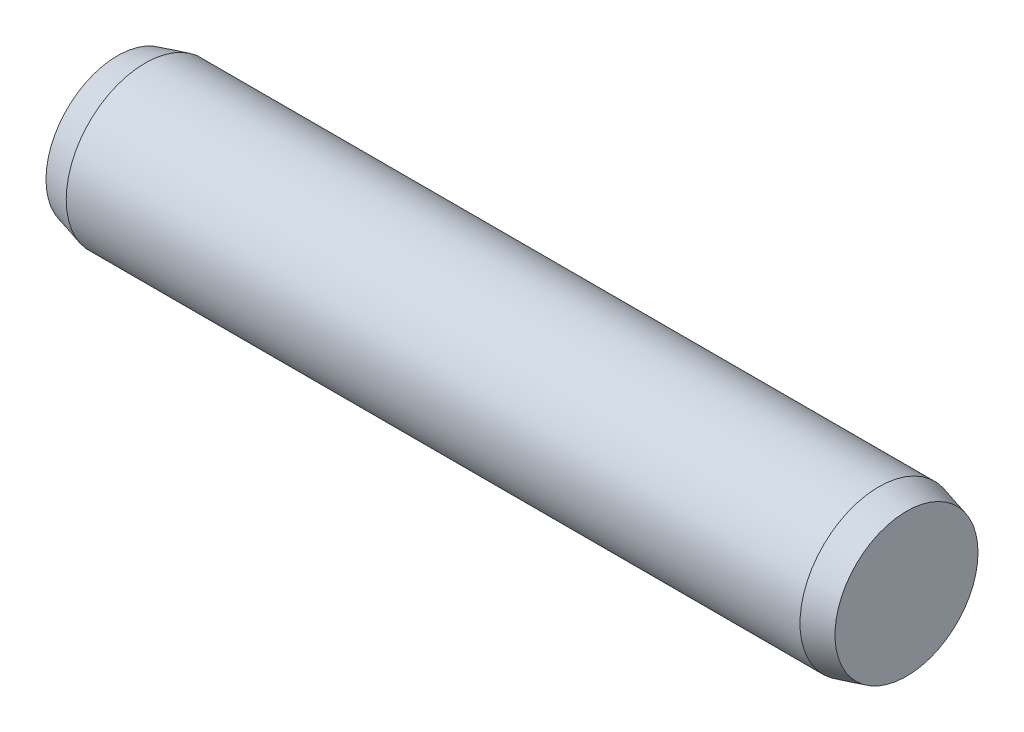
SolidWorks part; units mm, degrees
ref_plane "Front Plane" through (0, 0, 0) normal (0, 0, 1) x (1, 0, 0)
ref_plane "Top Plane" through (0, 0, 0) normal (0, 1, 0) x (1, 0, 0)
ref_plane "Right Plane" through (0, 0, 0) normal (1, 0, 0) x (0, 0, -1)
sketch "Sketch1" plane through (0, 0, 0) normal (0, 0, 1) x (1, 0, 0)
  line L0 (-4.65, 0) -> (4.65, 0) construction
  line L1 (4.65, 1) -> (4.65, -1) construction
  line L2 (-4.65, 1) -> (-4.65, -1) construction
  line L3 (5, 1) -> (5, -1) construction
  line L4 (-5, 1) -> (-5, -1) construction
  line L5 (-4.65, 0) -> (-5, 0) construction
  line L6 (4.65, 0) -> (5, 0) construction
  dimension "Dia" = 2
  dimension "C" = 0.35
  dimension "D1" = 0.35
  dimension "Length" = 10
sketch "Sketch2" plane through (0, 0, 0) normal (1, 0, 0) x (0, 0, -1)
  circle A0 centre (0, 0) radius 1
extrude "Extrude1" add sketch "Sketch2" against normal up to vertex (4.65 mm away) and the other way up to vertex (4.65 mm away) up to point (-4.65, 1, 0) other way up to point (4.65, 1, 0)
sketch "Sketch3" plane through (4.65, 0, 0) normal (1, 0, 0) x (0, 0, -1)
  circle A1 centre (0, 0) radius 1
  circle A2 centre (0, 0) radius 1
  dimension "D1" = 0
extrude "Extrude2" add sketch "Sketch3" along normal up to vertex (0.35 mm away) draft 15 up to point (5, 0, 0)
sketch "Sketch4" plane through (-4.65, 0, 0) normal (-1, 0, 0) x (0, 0, 1)
  circle A1 centre (0, 0) radius 1
  circle A2 centre (0, 0) radius 1
  dimension "D1" = 0
extrude "Extrude3" add sketch "Sketch4" along normal up to vertex (0.35 mm away) draft 15 up to point (-5, 0, 0)
equation "\"D1@Sketch1\" = \"C@Sketch1\""
